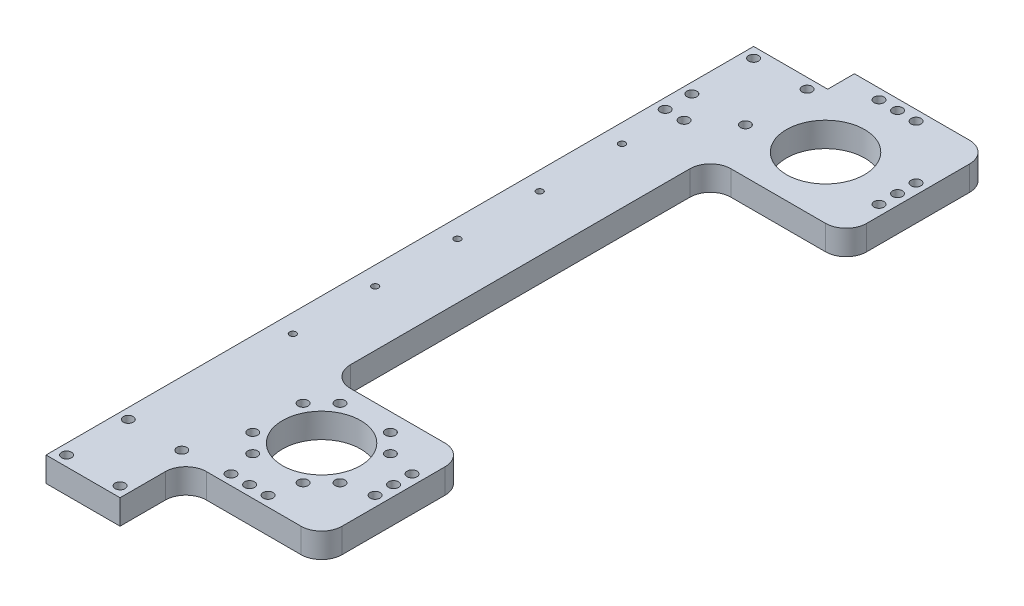
SolidWorks part; units mm, degrees
material "1060 Alloy"
ref_plane "Front Plane" through (0, 0, 0) normal (0, 0, 1) x (1, 0, 0)
ref_plane "Top Plane" through (0, 0, 0) normal (0, 1, 0) x (1, 0, 0)
ref_plane "Right Plane" through (0, 0, 0) normal (1, 0, 0) x (0, 0, -1)
sketch "Sketch1" plane through (0, 0, 0) normal (0, 1, 0) x (1, 0, 0)
  line L0 (9, 0) -> (9, 172) construction
  line L1 (0, 0) -> (18, 0)
  line L2 (0, 0) -> (0, 172)
  line L3 (0, 172) -> (18, 172)
  line L4 (18, 0) -> (18, 172)
  dimension "D1" = 18
  dimension "D2" = 172
extrude "Boss-Extrude1" add sketch "Sketch1" along normal blind 6
sketch "Sketch3" plane through (18, 0, 0) normal (1, 0, 0) x (0, 0, -1)
  line L0 (0, 0) -> (172, 0) construction
  line L1 (51, 0) -> (16, 0)
  line L2 (16, 0) -> (16, 6)
  line L3 (16, 6) -> (51, 6)
  line L4 (51, 0) -> (51, 6)
  line L5 (0, 6) -> (172, 6) construction
  line L8 (178.5, 0) -> (143.5, 0)
  line L9 (178.5, 0) -> (178.5, 6)
  line L10 (178.5, 6) -> (143.5, 6)
  line L11 (143.5, 0) -> (143.5, 6)
  line L12 (36, 6) -> (36, 0) construction
  line L13 (0, 6) -> (0, 0) construction
  line L14 (158.5, 6) -> (158.5, 0) construction
  line L15 (172, 6) -> (172, 0) construction
  dimension "D1" = 36
  dimension "D2" = 15
  dimension "D3" = 15
  dimension "D4" = 13.5
  dimension "D5" = 20
  dimension "D6" = 20
extrude "Boss-Extrude2" add sketch "Sketch3" along normal blind 32.98
sketch "Sketch2" plane through (0, 6, 0) normal (0, 1, 0) x (1, 0, 0)
  line L0 (0, 172) -> (0, 0) construction
  line L1 (30.98, 172) -> (30.98, 20.5428) construction
  line L2 (50.98, 36) -> (30.98, 36) construction
  line L4 (50.98, 158.5) -> (30.98, 158.5) construction
  line L6 (50.98, 51) -> (50.98, 16) construction
  line L7 (0, 0) -> (18, 0) construction
  line L8 (50.98, 178.5) -> (50.98, 143.5) construction
  line L9 (18, 172) -> (0, 172) construction
  circle A0 centre (30.98, 36) radius 9.5
  circle A2 centre (30.98, 158.5) radius 9.5
  dimension "D2" = 19
  dimension "D1" = 36
  dimension "D3" = 30.98
  dimension "D4" = 13.5
extrude "Cut-Extrude1" cut sketch "Sketch2" against normal through all
fillet "Fillet1" radius 5 7 edges at (50.98, 3, -51) (50.98, 3, -178.5) (50.98, 3, -143.5) (18, 3, -143.5) (50.98, 3, -16)
hole_wizard "M2 Tapped Hole1" positions "Sketch6" profile "Sketch5" tap size "M2" standard "ISO" end condition through all
sketch "Sketch6" plane through (0, 6, 0) normal (0, 1, 0) x (-1, 0, 0)
  line L0 (0, 0) -> (-18, 0) construction
  line L1 (0, -172) -> (0, 0) construction
  point P0 (-4.5, -55.5)
  point P17 (-4.5, -75.5)
  point P18 (-4.5, -95.5)
  point P19 (-4.5, -115.5)
  point P20 (-4.5, -135.5)
  dimension "D1" = 55.5
  dimension "D3" = 4.5
  dimension "D2" = 5
sketch "Sketch5" plane through (4.5, 6, -55.5) normal (1, 0, 0) x (0, 0, 1)
  line L0 (0, 0) -> (0, 6)
  line L1 (0, 6) -> (0.8, 6)
  line L2 (0.8, 6) -> (0.8, 0)
  line L5 (0.8, 0) -> (0, 0)
  line L11 (0, -6.35) -> (0, 107.95) construction
  dimension "Thru Tap Drill Dia." = 1.6
  dimension "Thru Tap Drill Depth" = 6
cosmetic thread "Hole Thread1" parameters "D2"=2
cosmetic thread "Hole Thread2" parameters "D2"=2
cosmetic thread "Hole Thread3" parameters "D2"=2
cosmetic thread "Hole Thread4" parameters "D2"=2
cosmetic thread "Hole Thread5" parameters "D2"=2
hole_wizard "M2 Clearance Hole1" positions "3DSketch1" profile "Sketch7" hole size "M2" standard "ISO" end condition through all
sketch3d "3DSketch1"
  line L5 (45.98, 6, -16) -> (23, 6, -16) construction
  line L6 (50.98, 6, -46) -> (50.98, 6, -21) construction
  line L14 (45.98, 6, -178.5) -> (18, 6, -178.5) construction
  point P28 (48.48, 6, -40.5)
  point P31 (26.48, 6, -18.5)
  point P33 (30.98, 6, -18.5)
  point P35 (35.48, 6, -18.5)
  point P37 (48.48, 6, -36)
  point P39 (48.48, 6, -31.5)
  point P63 (26.48, 6, -176)
  point P65 (30.98, 6, -176)
  point P67 (35.48, 6, -176)
  point P69 (48.48, 6, -154)
  point P71 (48.48, 6, -158.5)
  point P73 (48.48, 6, -163)
  dimension "D1" = 2.5
  dimension "D3" = 4.5
  dimension "D2" = 2.5
  dimension "D4" = 4.5
  dimension "D5" = 15.5
  dimension "D6" = 15.5
  dimension "D7" = 4.5
  dimension "D8" = 4.5
  dimension "D9" = 2.5
  dimension "D10" = 4.5
  dimension "D12" = 15.5
  dimension "D11" = 4.5
sketch "Sketch7" plane through (48.48, 6, -40.5) normal (1, 0, 0) x (0, 0, 1)
  line L0 (0, 0) -> (0, 6)
  line L1 (0, 6) -> (1.2, 6)
  line L2 (1.2, 6) -> (1.2, 0)
  line L5 (1.2, 0) -> (0, 0)
  line L11 (0, -6.35) -> (0, 107.95) construction
  dimension "Thru Hole Dia." = 2.4
  dimension "Thru Hole Depth" = 6
hole_wizard "M2 Clearance Hole2" positions "Sketch10" profile "Sketch9" hole size "M2" standard "ISO" end condition through all
sketch "Sketch10" plane through (0, 6, 0) normal (0, 1, 0) x (-1, 0, 0)
  line L0 (0, 0) -> (-18, 0) construction
  line L1 (-9, 0) -> (-9, -23.5195) construction
  line L3 (0, -10) -> (-14.1227, -10) construction
  line L4 (0, -172) -> (0, 0) construction
  line L6 (0, -86) -> (-18, -86) construction
  line L7 (-18, -56) -> (-18, -138.5) construction
  point P0 (-2.5, -2.5)
  point P16 (-15.5, -2.5)
  point P18 (-15.5, -17.5)
  point P19 (-2.5, -17.5)
  point P25 (-15.5, -154.5)
  point P26 (-15.5, -169.5)
  point P27 (-2.5, -154.5)
  point P28 (-2.5, -169.5)
  dimension "D1" = 2.5
  dimension "D2" = 7.5
  dimension "D3" = 6.5
sketch "Sketch9" plane through (2.5, 6, -2.5) normal (1, 0, 0) x (0, 0, 1)
  line L0 (0, 0) -> (0, 6)
  line L1 (0, 6) -> (1.2, 6)
  line L2 (1.2, 6) -> (1.2, 0)
  line L5 (1.2, 0) -> (0, 0)
  line L11 (0, -6.35) -> (0, 107.95) construction
  dimension "Thru Hole Dia." = 2.4
  dimension "Thru Hole Depth" = 6
hole_wizard "M2 Clearance Hole3" positions "Sketch12" profile "Sketch11" hole size "M2" standard "ISO" end condition through all
sketch "Sketch12" plane through (0, 6, 0) normal (0, 1, 0) x (-1, 0, 0)
  circle A1 centre (-4.5, -135.5) radius 0.8 construction
  point P20 (-2.5, -148)
  point P32 (-7.1, -148)
  dimension "D1" = 2
  dimension "D3" = 4.6
  dimension "D2" = 12.5
sketch "Sketch11" plane through (2.5, 6, -148) normal (1, 0, 0) x (0, 0, 1)
  line L0 (0, 0) -> (0, 6)
  line L1 (0, 6) -> (1.2, 6)
  line L2 (1.2, 6) -> (1.2, 0)
  line L5 (1.2, 0) -> (0, 0)
  line L11 (0, -6.35) -> (0, 107.95) construction
  dimension "Thru Hole Dia." = 2.4
  dimension "Thru Hole Depth" = 6
hole_wizard "M2 Clearance Hole4" positions "Sketch14" profile "Sketch13" hole size "M2" standard "ISO" end condition through all
sketch "Sketch14" plane through (0, 6, 0) normal (0, 1, 0) x (-1, 0, 0)
  line L0 (-20.3712, -42.125) -> (-41.5888, -29.875) construction
  line L2 (-37.105, -25.3912) -> (-24.855, -46.6088) construction
  line L4 (-20.3712, -29.875) -> (-41.5888, -42.125) construction
  line L7 (-37.105, -46.6088) -> (-24.855, -25.3912) construction
  line L9 (-30.98, -48.25) -> (-30.98, -23.75) construction
  circle A0 centre (-30.98, -36) radius 12.25 construction
  point P0 (-20.3712, -29.875)
  point P1 (-24.855, -25.3912)
  point P3 (-20.3712, -42.125)
  point P5 (-24.855, -46.6088)
  point P7 (-37.105, -46.6088)
  point P9 (-41.5888, -42.125)
  point P11 (-41.5888, -29.875)
  point P13 (-37.105, -25.3912)
  dimension "D1" = 24.5
  dimension "D2" = 30
  dimension "D3" = 60
  dimension "D4" = 30
  dimension "D5" = 30
sketch "Sketch13" plane through (20.3712, 6, -29.875) normal (1, 0, 0) x (0, 0, 1)
  line L0 (0, 0) -> (0, 6)
  line L1 (0, 6) -> (1.2, 6)
  line L2 (1.2, 6) -> (1.2, 0)
  line L5 (1.2, 0) -> (0, 0)
  line L11 (0, -6.35) -> (0, 107.95) construction
  dimension "Thru Hole Dia." = 2.4
  dimension "Thru Hole Depth" = 6
equation "\"D4@3DSketch1\" = \"D3@3DSketch1\""
equation "\"D7@3DSketch1\" = \"D3@3DSketch1\""
equation "\"D8@3DSketch1\" = \"D3@3DSketch1\""
equation "\"D9@3DSketch1\" = \"D1@3DSketch1\""
equation "\"D10@3DSketch1\" = \"D3@3DSketch1\""
equation "\"D11@3DSketch1\" = \"D10@3DSketch1\""
equation "\"D12@3DSketch1\" = \"D6@3DSketch1\""
